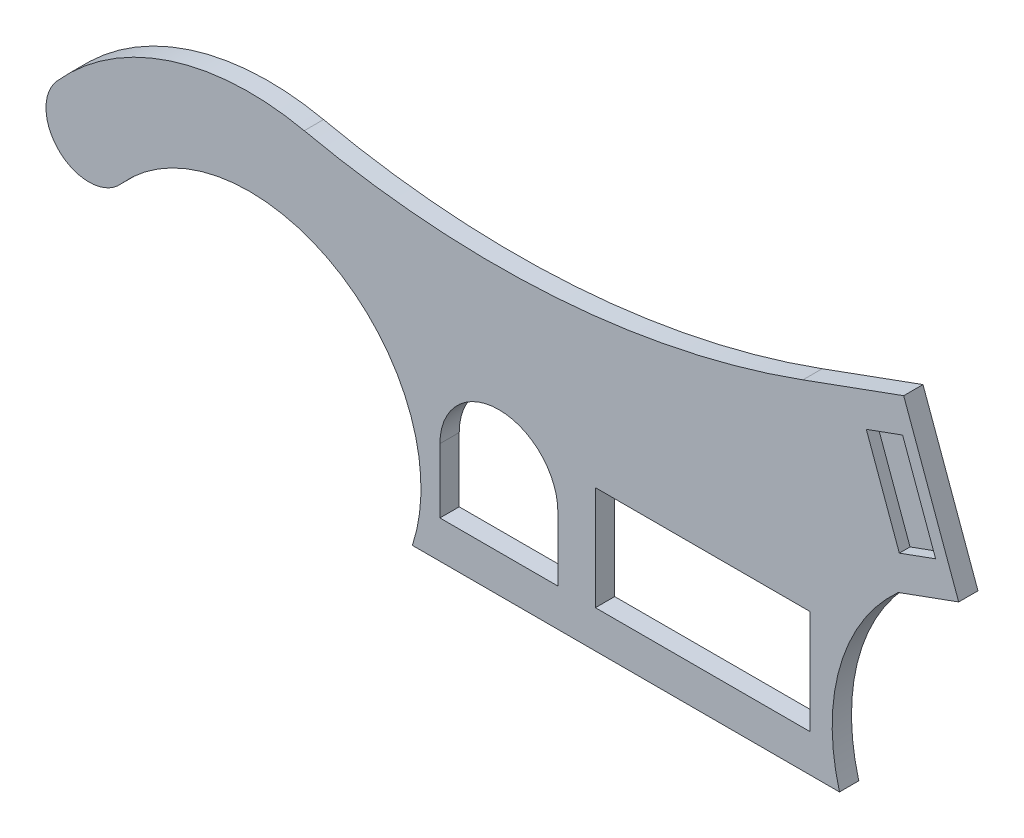
SolidWorks part; units mm, degrees
ref_plane "Спереди" through (0, 0, 0) normal (0, 0, 1) x (1, 0, 0)
ref_plane "Сверху" through (0, 0, 0) normal (0, 1, 0) x (1, 0, 0)
ref_plane "Справа" through (0, 0, 0) normal (1, 0, 0) x (0, 0, -1)
sketch "Sketch1" plane through (0, 0, 0) normal (0, 0, 1) x (1, 0, 0)
  line L0 (0, 0) -> (51.303, -140.9539)
  line L1 (-1000, 0) -> (49000, 0) construction
  line L2 (10.6418, 0) -> (119.8328, -300) construction
  line L3 (0, 0) -> (-93.9693, -34.202)
  line L4 (-458.1803, -350) -> (-59.8669, -350)
  line L5 (51.303, -140.9539) -> (-5.0785, -161.4751)
  circle A0 centre (119.8328, -300) radius 127.5 construction
  circle A1 centre (-610.1672, -300) radius 127.5 construction
  arc A3 (-458.1803, -350) -> (-729.9368, -193.9094) centre (-610.1672, -300) ccw
  arc A4 (-729.9368, -193.9094) -> (-789.8217, -140.864) centre (-759.8792, -167.3867) cw
  arc A5 (-789.8217, -140.864) -> (-559.0472, -65.5075) centre (-610.1672, -300) cw
  arc A6 (-559.0472, -65.5075) -> (-93.9693, -34.202) centre (-380.5645, 753.2118) ccw
  arc A7 (-59.8669, -350) -> (-5.0785, -161.4751) centre (119.8328, -300) cw
  point P19 (-19.4987, -166.7236)
  dimension "D3" = 255
  dimension "D4" = 255
  dimension "D10" = 40
  dimension "D11" = 160
  dimension "D1" = 150
  dimension "D2" = 110
  dimension "D5" = 300
  dimension "D6" = 300
  dimension "D7" = 730
  dimension "D8" = 10
  dimension "D9" = 100
  dimension "D12" = 350
  dimension "D13" = 60
extrude "Boss-Extrude1" add sketch "Sketch1" along normal blind 18
sketch "Sketch2" plane through (0, 0, 18) normal (0, 0, 1) x (1, 0, 0)
  line L0 (-458.1803, -350) -> (-59.8669, -350) construction
  line L1 (-287.5083, -315) -> (-87.5083, -315)
  line L2 (-287.5083, -315) -> (-287.5083, -218)
  line L3 (-287.5083, -218) -> (-87.5083, -218)
  line L4 (-87.5083, -315) -> (-87.5083, -218)
  line L5 (-287.5083, -315) -> (-87.5083, -218) construction
  line L6 (-287.5083, -218) -> (-87.5083, -315) construction
  line L7 (-322.5083, -315) -> (-432.5083, -315)
  line L8 (-322.5083, -315) -> (-322.5083, -255)
  line L9 (-432.5083, -315) -> (-432.5083, -255)
  arc A0 (-432.5083, -255) -> (-322.5083, -255) centre (-377.5083, -255) cw
  point P0 (-187.5083, -266.5)
  point P12 (-399.5514, -310.099)
  point P13 (-332.2847, -310.099)
  point P14 (-408.1389, -310.099)
  point P15 (-208.6434, -266.5)
  point P16 (-200.6372, -266.5)
  dimension "D1" = 200
  dimension "D2" = 97
  dimension "D3" = 35
  dimension "D4" = 110
  dimension "D5" = 60
  dimension "D6" = 60
  dimension "D7" = 35
extrude "Cut-Extrude1" cut sketch "Sketch2" against normal through all
sketch "Sketch3" plane through (0, 0, 18) normal (0, 0, 1) x (1, 0, 0)
  line L0 (-1.0157, -32.295) -> (29.7661, -116.8674)
  line L1 (-1.0157, -32.295) -> (-34.8446, -44.6077)
  line L2 (29.7661, -116.8674) -> (-4.0628, -129.1801)
  line L3 (-34.8446, -44.6077) -> (-4.0628, -129.1801)
  line L5 (51.303, -140.9539) -> (0, 0) construction
  line L6 (0, 0) -> (-93.9693, -34.202) construction
  line L7 (-5.0785, -161.4751) -> (51.303, -140.9539) construction
  line L8 (-17.9302, -38.4514) -> (12.8516, -123.0237) construction
  dimension "D1" = 36
  dimension "D2" = 30
  dimension "D3" = 30
  dimension "D4" = 30
extrude "Cut-Extrude2" cut sketch "Sketch3" against normal blind 10
